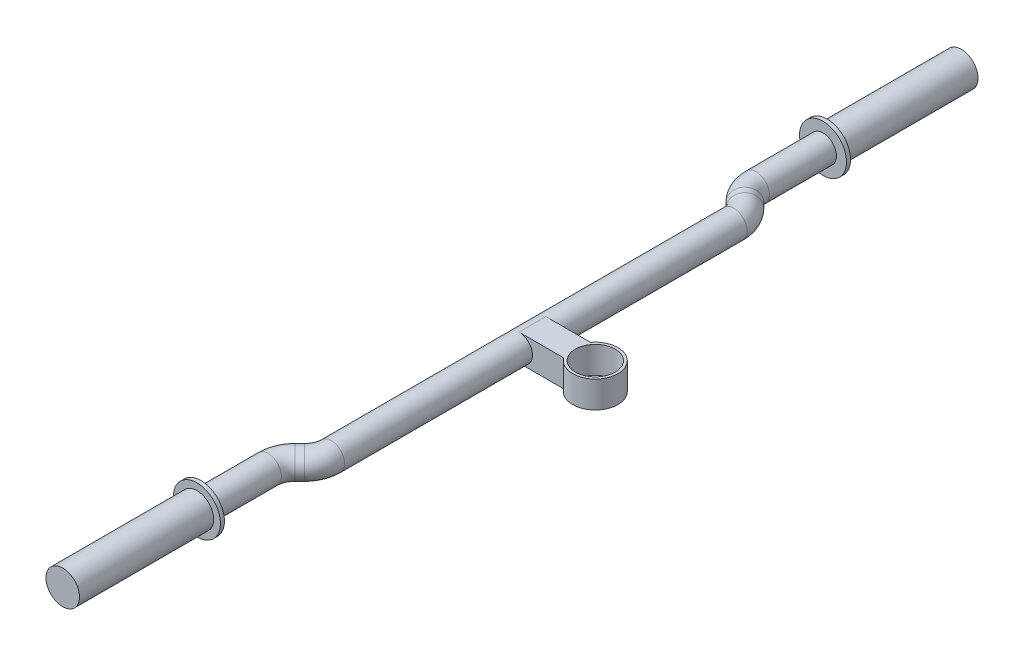
SolidWorks part; units mm, degrees
ref_plane "Front Plane" through (0, 0, 0) normal (0, 0, 1) x (1, 0, 0)
ref_plane "Top Plane" through (0, 0, 0) normal (0, 1, 0) x (1, 0, 0)
ref_plane "Right Plane" through (0, 0, 0) normal (1, 0, 0) x (0, 0, -1)
sketch "Sketch1" plane through (0, 0, 0) normal (0, 1, 0) x (1, 0, 0)
  circle A0 centre (0, 0) radius 14.85
  circle A1 centre (0, 0) radius 16.85
  dimension "D1" = 33.7
  dimension "D2" = 29.7
extrude "Boss-Extrude1" add sketch "Sketch1" along normal blind 20
sketch "Sketch2" plane through (0, 0, 0) normal (0, 0, 1) x (1, 0, 0)
  line L0 (-16.85, 20) -> (-16.85, 0) construction
  circle A0 centre (-46.85, 10) radius 10
  point P4 (-16.85, 10)
  dimension "D1" = 20
  dimension "D2" = 30
sketch "Sketch3" plane through (0, 0, 0) normal (0, 1, 0) x (1, 0, 0)
  line L0 (-46.85, 0) -> (-46.85, -150)
  line L1 (-56.85, 0) -> (-36.85, 0) construction
  line L2 (-52.7079, -164.1421) -> (-56.2434, -167.6777)
  line L3 (-62.1013, -181.8198) -> (-62.1013, -231.8198)
  arc A0 (-56.2434, -167.6777) -> (-62.1013, -181.8198) centre (-42.1013, -181.8198) ccw
  arc A1 (-46.85, -150) -> (-52.7079, -164.1421) centre (-66.85, -150) cw
  dimension "D1" = 20
  dimension "D2" = 150
  dimension "D3" = 5
  dimension "D4" = 135
  dimension "D5" = 50
sweep "Sweep1" add profiles "Sketch2" path "Sketch3"
sketch "Sketch5" plane through (0, 0, 231.8198) normal (0, 0, 1) x (1, 0, 0)
  circle A0 centre (-62.1013, 10) radius 17.5
  dimension "D1" = 35
extrude "Boss-Extrude3" add sketch "Sketch5" along normal blind 3 separate body
sketch "Sketch6" plane through (0, 0, 234.8198) normal (0, 0, 1) x (1, 0, 0)
  circle A0 centre (-62.1013, 10) radius 12.5
  dimension "D1" = 25
extrude "Boss-Extrude4" add sketch "Sketch6" along normal blind 100
mirror "Mirror1" about plane through (-46.85, 10, 0) normal (0, 0, 1) of "Sweep1", "Boss-Extrude4", "Boss-Extrude3"
sketch "Sketch4" plane through (0, 20, 0) normal (0, 1, 0) x (1, 0, 0)
  line L5 (-13.5618, 10) -> (-46.85, 10)
  line L6 (-46.85, 10) -> (-46.85, -10)
  line L7 (-46.85, -10) -> (-13.5618, -10)
  line L8 (-56.85, 150) -> (-56.85, -150) construction
  circle A5 centre (0, 0) radius 16.85
  arc A6 (-13.5618, 10) -> (-13.5618, -10) centre (0, 0) ccw
  dimension "D2" = 10
  dimension "D3" = 10
  dimension "D4" = 10
  dimension "D1" = 0
extrude "Boss-Extrude2" add sketch "Sketch4" against normal up to surface (20 mm away) up to face at (0, 0, 16.85)
sketch "Sketch7" plane through (0, 0, -231.8198) normal (0, 0, -1) x (-1, 0, 0)
  circle A0 centre (62.1013, 10) radius 17.5
  dimension "D1" = 35
extrude "Boss-Extrude5" add sketch "Sketch7" along normal blind 3 separate body
sketch "Sketch8" plane through (0, 0, -234.8198) normal (0, 0, -1) x (-1, 0, 0)
  circle A0 centre (62.1013, 10) radius 12.5
  dimension "D1" = 25
extrude "Boss-Extrude6" add sketch "Sketch8" along normal blind 100
